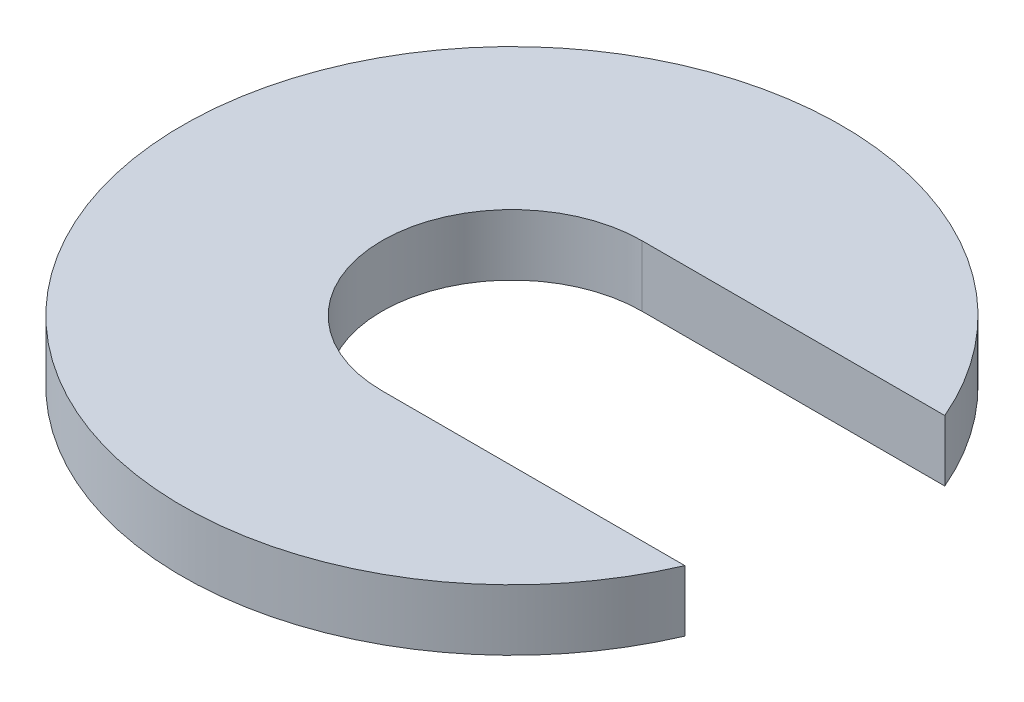
SolidWorks part; units mm, degrees
material "Bismuth"
ref_plane "Front" through (0, 0, 0) normal (0, 0, 1) x (1, 0, 0)
ref_plane "Top" through (0, 0, 0) normal (0, 1, 0) x (1, 0, 0)
ref_plane "Right" through (0, 0, 0) normal (1, 0, 0) x (0, 0, -1)
sketch "Sketch1" plane through (0, 0, 0) normal (0, 1, 0) x (1, 0, 0)
  line L0 (0, 29.575) -> (68.9226, 29.575)
  line L1 (0, -29.575) -> (68.9226, -29.575)
  arc A2 (68.9226, 29.575) -> (68.9226, -29.575) centre (0, 0) ccw
  arc A3 (0, 29.575) -> (0, -29.575) centre (0, 0) ccw
  point P2 (0, 0)
  point P3 (0, 0)
  point P5 (0, 0)
  point P6 (0, 0)
  point P10 (0, 0)
  point P11 (0, 0)
  point P12 (0, 0)
  point P13 (0, 0)
  point P14 (0, 0)
  point P15 (0, 0)
  point P16 (0, 0)
  point P17 (0, 0)
extrude "Boss-Extrude1" add sketch "Sketch1" along normal blind 13.9 contours A3 L1 A2 L0
